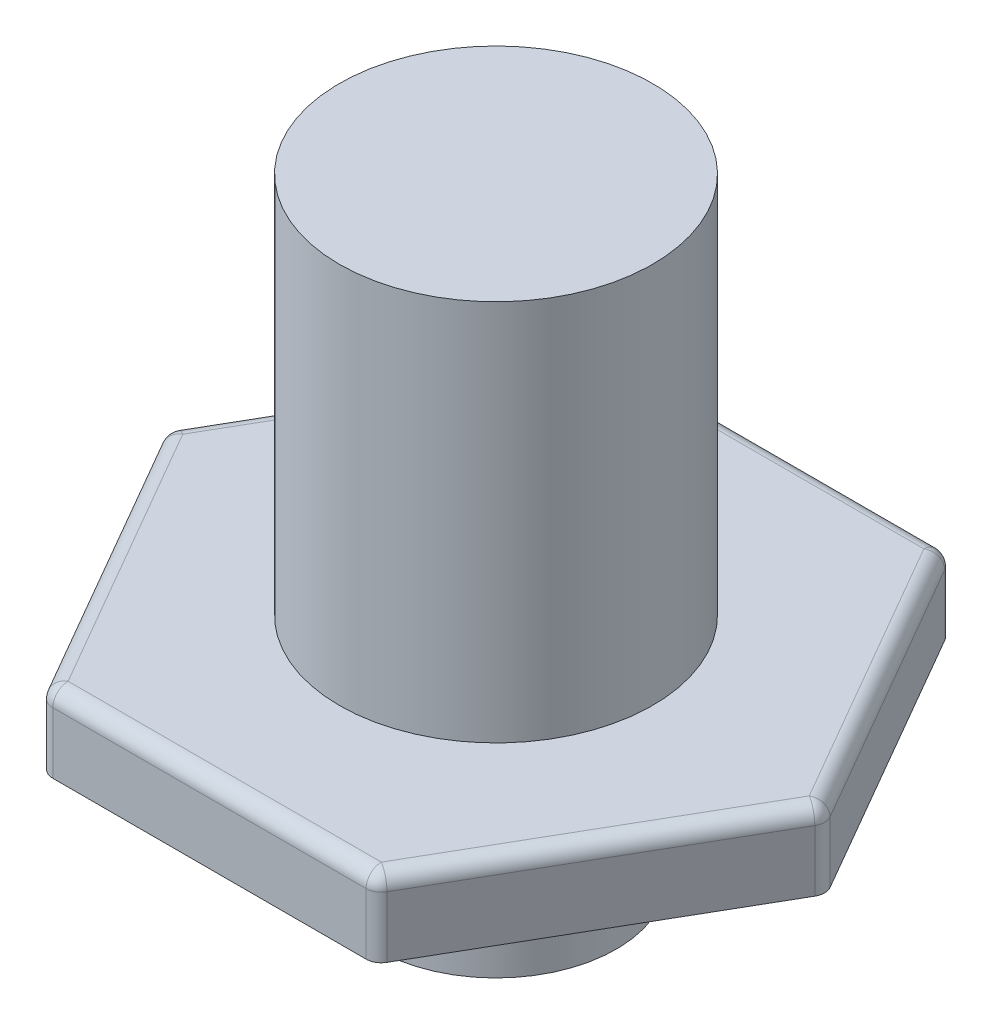
SolidWorks part; units mm, degrees
material "1060 Alloy"
ref_plane "Front Plane" through (0, 0, 0) normal (0, 0, 1) x (1, 0, 0)
ref_plane "Top Plane" through (0, 0, 0) normal (0, 1, 0) x (1, 0, 0)
ref_plane "Right Plane" through (0, 0, 0) normal (1, 0, 0) x (0, 0, -1)
sketch "Sketch1" plane through (0, 0, 0) normal (0, 1, 0) x (1, 0, 0)
  line L1 (10.9985, 0) -> (5.4993, 9.525)
  line L2 (5.4993, 9.525) -> (-5.4993, 9.525)
  line L3 (-5.4993, 9.525) -> (-10.9985, 0)
  line L4 (-10.9985, 0) -> (-5.4993, -9.525)
  line L5 (-5.4993, -9.525) -> (5.4993, -9.525)
  line L6 (5.4993, -9.525) -> (10.9985, 0)
  circle A0 centre (0, 0) radius 9.525 construction
  dimension "D1" = 19.05
extrude "Boss-Extrude1" add sketch "Sketch1" along normal blind 2.54
sketch "Sketch2" plane through (0, 2.54, 0) normal (0, 1, 0) x (1, 0, 0)
  circle A0 centre (0, 0) radius 5.207
  dimension "D1" = 10.414
extrude "Boss-Extrude2" add sketch "Sketch2" along normal blind 12.7
sketch "Sketch6" plane through (0, 0, 0) normal (0, -1, 0) x (-1, 0, 0)
  circle A0 centre (0, 0) radius 4
extrude "Boss-Extrude3" add sketch "Sketch6" along normal blind 5.08
fillet "Fillet1" radius 0.508 12 edges at (5.4993, 1.27, -9.525) (10.9985, 1.27, 0) (5.4993, 1.27, 9.525) (-5.4993, 1.27, 9.525) (-10.9985, 1.27, 0) (-5.4993, 1.27, -9.525) (0, 2.54, -9.525) (-8.2489, 2.54, -4.7625) (-8.2489, 2.54, 4.7625) (8.2489, 2.54, -4.7625) (0, 2.54, 9.525) (8.2489, 2.54, 4.7625)
chamfer "Chamfer1" [suppressed] distance 0.508 angle 45
sketch "Sketch3" plane through (0, 15.24, 0) normal (0, 1, 0) x (1, 0, 0)
  circle A0 centre (0, 0) radius 3.175
  dimension "D1" = 6.35
extrude "Cut-Extrude1" [suppressed] cut sketch "Sketch3" against normal blind 15.875
hole_wizard "3/8 (0.3750) Dowel Hole1" [suppressed] positions "Sketch4" profile "Sketch5" hole size "3/8" standard "ANSI Inch"
sketch "Sketch4" plane through (0, 0, 0) normal (0, -1, 0) x (-1, 0, 0)
  point P0 (0, 0)
sketch "Sketch5" plane through (0, 0, 0) normal (1, 0, 0) x (0, 0, -1)
  line L0 (0, 0) -> (0, 16.0337)
  line L1 (0, 16.0337) -> (4.7625, 16.0337)
  line L2 (4.7625, 16.0337) -> (4.7625, 0)
  line L5 (4.7625, 0) -> (0, 0)
  line L11 (0, -6.35) -> (0, 107.95) construction
  dimension "Thru Hole Dia." = 9.525
  dimension "Thru Hole Depth" = 16.0337
